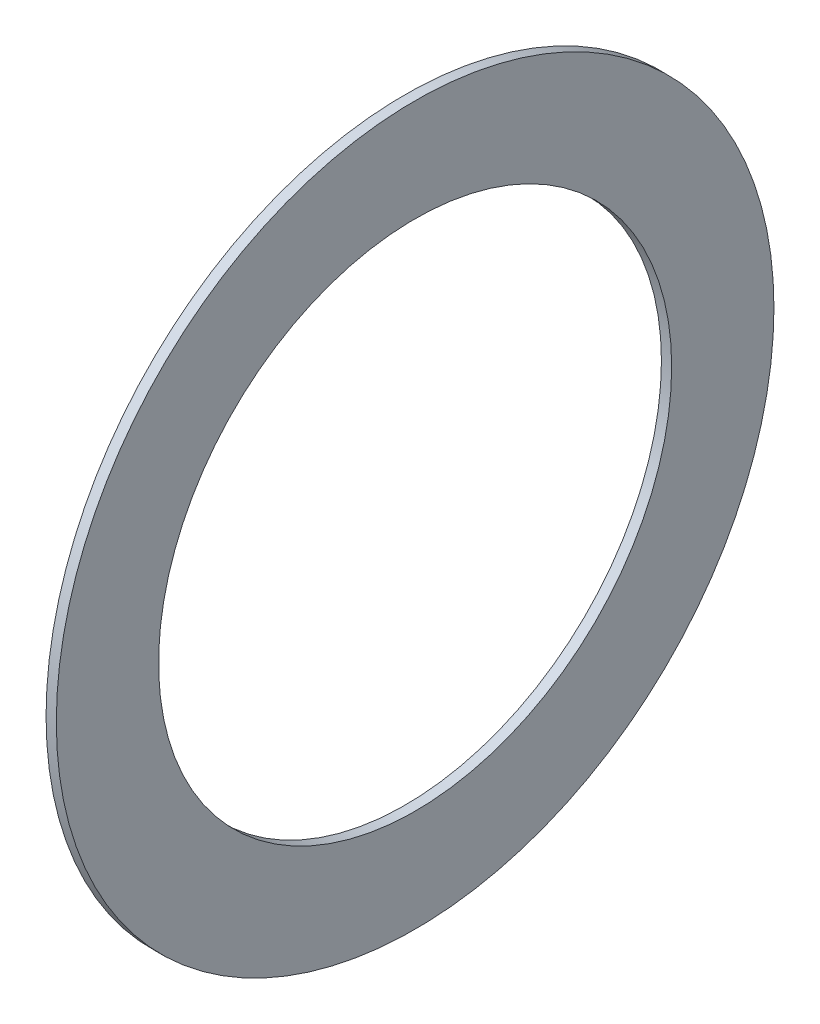
SolidWorks part; units mm, degrees
material "AISI 1020"
ref_plane "Front Plane" through (0, 0, 0) normal (0, 0, 1) x (1, 0, 0)
ref_plane "Top Plane" through (0, 0, 0) normal (0, 1, 0) x (1, 0, 0)
ref_plane "Right Plane" through (0, 0, 0) normal (1, 0, 0) x (0, 0, -1)
sketch "Sketch1" plane through (0, 0, 0) normal (1, 0, 0) x (0, 0, -1)
  circle A0 centre (0, 0) radius 35
  circle A1 centre (0, 0) radius 25 construction
  circle A2 centre (0, 0) radius 25.025
  dimension "OD" = 70
  dimension "For Shaft Diameter" = 50
  dimension "ID" = 50.05
sketch "Sketch2" plane through (0, 0, 0) normal (0, 0, 1) x (1, 0, 0)
  line L0 (0.5, 0) -> (-0.5, 0) construction
  line L1 (0.5, -35) -> (-0.5, -35) construction
  line L2 (0.5, -35) -> (0.5, 35) construction
  line L3 (0.5, 35) -> (-0.5, 35) construction
  line L4 (-0.5, -35) -> (-0.5, 35) construction
  point P6 (0, 35)
  point P9 (0, -35)
  dimension "Thickness" = 1
sketch "Sketch3" plane through (0, 0, 0) normal (1, 0, 0) x (0, 0, -1)
  circle A1 centre (0, 0) radius 35 construction
  circle A3 centre (0, 0) radius 35
  circle A4 centre (0, 0) radius 25.025 construction
  circle A5 centre (0, 0) radius 25.025
extrude "Boss-Extrude1" add sketch "Sketch3" along normal up to vertex (0.5 mm away) and the other way up to vertex (0.5 mm away) up to point (0.5, 35, 0) other way up to point (-0.5, 35, 0)
